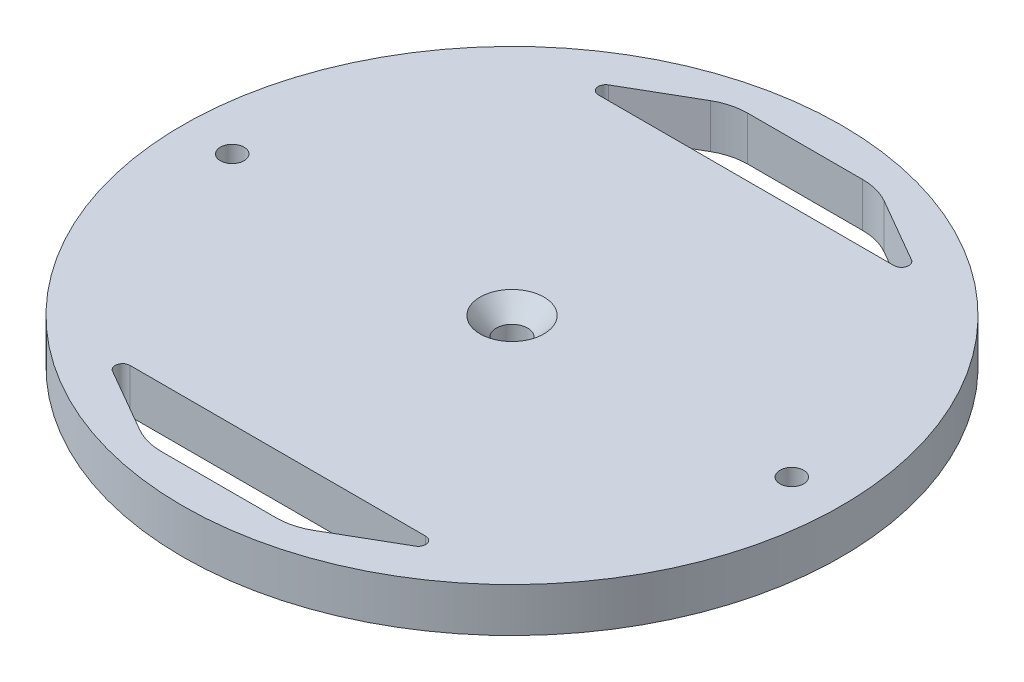
SolidWorks part; units mm, degrees
material "6061 Alloy"
ref_plane "Front Plane" through (0, 0, 0) normal (0, 0, 1) x (1, 0, 0)
ref_plane "Top Plane" through (0, 0, 0) normal (0, 1, 0) x (1, 0, 0)
ref_plane "Right Plane" through (0, 0, 0) normal (1, 0, 0) x (0, 0, -1)
sketch "Sketch2" plane through (0, 0, 0) normal (0, 1, 0) x (1, 0, 0)
  circle A0 centre (0, 0) radius 71.0565
  dimension "D1" = 142.113
extrude "Boss-Extrude1" add sketch "Sketch2" along normal blind 9.525
sketch "Sketch3" plane through (0, 9.525, 0) normal (0, 1, 0) x (1, 0, 0)
  point P0 (-60.325, 0)
  point P1 (60.325, 0)
  dimension "D1" = 60.325
  dimension "D2" = 60.325
hole_wizard "Tap Drill for 1/4-20 Tap1" positions "Sketch3" profile "Sketch4" hole size "1/4-20" standard "ANSI Inch" end condition through all
sketch "Sketch4" plane through (-60.325, 9.525, 0) normal (1, 0, 0) x (0, 0, 1)
  line L0 (0, 0) -> (0, 9.525)
  line L1 (0, 9.525) -> (2.5527, 9.525)
  line L2 (2.5527, 9.525) -> (2.5527, 0)
  line L5 (2.5527, 0) -> (0, 0)
  line L11 (0, -6.35) -> (0, 107.95) construction
  dimension "Thru Hole Dia." = 5.1054
  dimension "Thru Hole Depth" = 9.525
sketch "Sketch5" plane through (0, 9.525, 0) normal (0, 1, 0) x (1, 0, 0)
  point P0 (0, 0)
hole_wizard "CSK for 1/4 Flat Head Machine Screw1" positions "Sketch5" profile "Sketch7" countersink size "1/4" standard "ANSI Inch" end condition through all
sketch "Sketch7" plane through (0, 9.525, 0) normal (1, 0, 0) x (0, 0, 1)
  line L0 (0, 0) -> (0, 9.525)
  line L1 (0, 9.525) -> (3.3782, 9.525)
  line L2 (3.3782, 9.525) -> (3.3782, 4.0323)
  line L3 (3.3782, 4.0323) -> (6.8834, 0)
  line L5 (6.8834, 0) -> (0, 0)
  line L6 (-3.3782, 4.0323) -> (-6.8834, 0) construction
  line L11 (0, -6.35) -> (0, 107.95) construction
  dimension "Thru Hole Dia." = 6.7564
  dimension "Thru Hole Depth" = 9.525
  dimension "Near C'Sink Dia." = 13.7668
  dimension "Near C'Sink Angle" = 82
sketch "Sketch8" plane through (0, 9.525, 0) normal (0, 1, 0) x (1, 0, 0)
  line L0 (-37.8, 50.5) -> (-15.803, 63.2)
  line L1 (-50.5, -50.5) -> (50.5, -50.5) construction
  line L2 (-50.5, -50.5) -> (-50.5, 50.5) construction
  line L3 (-50.5, 50.5) -> (50.5, 50.5) construction
  line L4 (50.5, -50.5) -> (50.5, 50.5) construction
  line L5 (-50.5, -50.5) -> (50.5, 50.5) construction
  line L6 (-50.5, 50.5) -> (50.5, -50.5) construction
  line L7 (-15.803, 63.2) -> (15.803, 63.2)
  line L8 (15.803, 63.2) -> (37.8, 50.5)
  line L9 (37.8, 50.5) -> (-37.8, 50.5)
  line L10 (-60.325, 0) -> (60.325, 0) construction
  point P2 (0, 0)
  dimension "D1" = 101
  dimension "D2" = 101
  dimension "D3" = 12.7
  dimension "D4" = 12.7
  dimension "D5" = 12.7
  dimension "D6" = 30
  dimension "D7" = 30
extrude "Cut-Extrude1" cut sketch "Sketch8" against normal through all both and the other way through all
fillet "Fillet1" radius 12.7 2 edges at (15.803, 4.7625, -63.2) (-15.803, 4.7625, -63.2)
fillet "Fillet2" radius 1.5875 2 edges at (37.8, 4.7625, -50.5) (-37.8, 4.7625, -50.5)
mirror "Mirror1" about plane through (0, 0, 0) normal (0, 0, 1) of "Fillet1", "Cut-Extrude1", "Fillet2"
equation "\"outerdiameter\"= 5.595"
equation "\"platethickness\"= 3 / 8"
equation "\"holespacing\"= 2.375"
equation "\"D1@Sketch2\"=\"outerdiameter\""
equation "\"D1@Boss-Extrude1\"=\"platethickness\""
equation "\"D2@Sketch3\"=\"holespacing\""
equation "\"D1@Sketch3\"=\"holespacing\""
